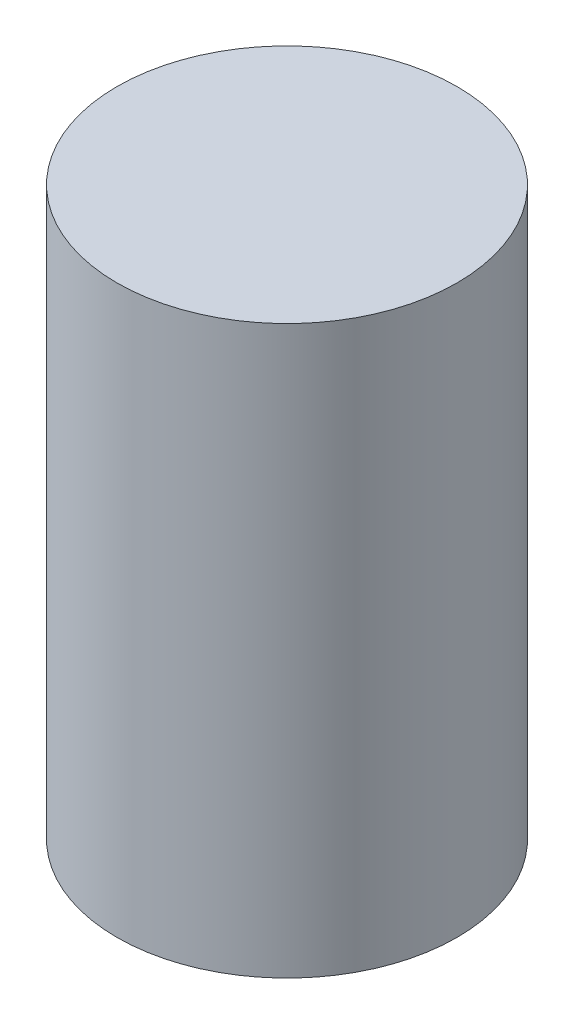
SolidWorks part; units mm, degrees
material "AISI 304"
ref_plane "Front Plane" through (0, 0, 0) normal (0, 0, 1) x (1, 0, 0)
ref_plane "Top Plane" through (0, 0, 0) normal (0, 1, 0) x (1, 0, 0)
ref_plane "Right Plane" through (0, 0, 0) normal (1, 0, 0) x (0, 0, -1)
sketch "Sketch1" plane through (0, 0, 0) normal (0, 1, 0) x (1, 0, 0)
  circle A0 centre (0, 0) radius 1.5
extrude "Boss-Extrude1" add sketch "Sketch1" along normal blind 5
